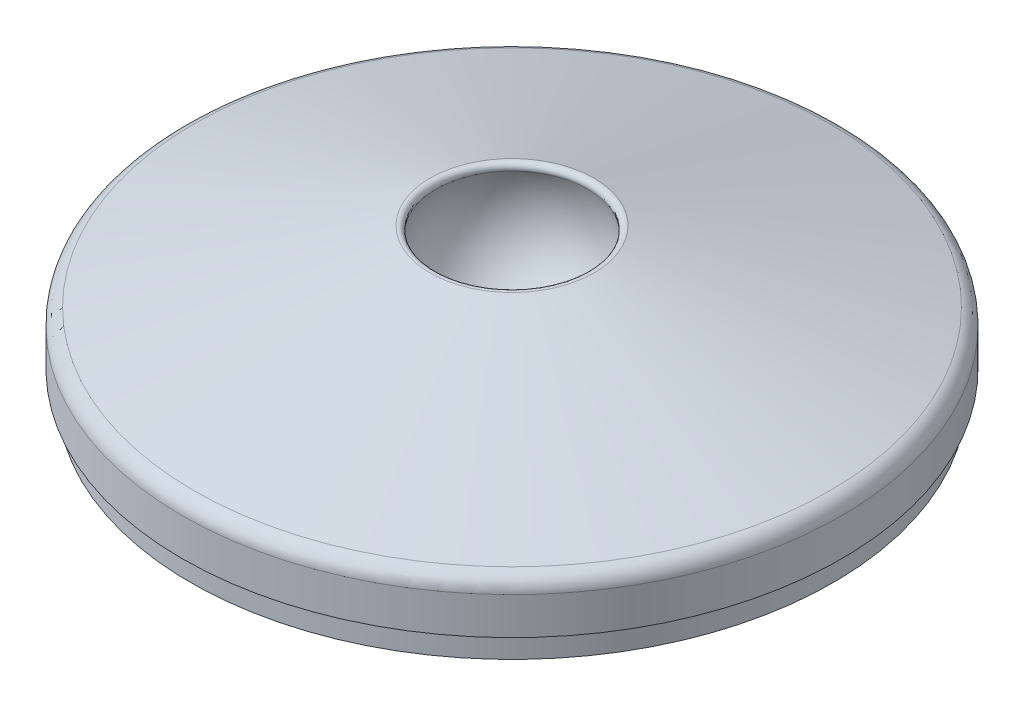
SolidWorks part; units mm, degrees
ref_plane "Front Plane" through (0, 0, 0) normal (0, 0, 1) x (1, 0, 0)
ref_plane "Top Plane" through (0, 0, 0) normal (0, 1, 0) x (1, 0, 0)
ref_plane "Right Plane" through (0, 0, 0) normal (1, 0, 0) x (0, 0, -1)
sketch "Sketch2" plane through (0, 0, 0) normal (0, 0, 1) x (1, 0, 0)
  line L0 (0, 35.0246) -> (0, -24.0887) construction
  line L1 (0, 0) -> (-20, 0)
  line L2 (-20, 0) -> (-20, 3.0049)
  line L3 (-20, 3.0049) -> (0, 9.0148)
  line L4 (0, 0) -> (0, 9.0148)
  dimension "D1" = 40
revolve "Revolve1" add sketch "Sketch2" angle 360 about L0
sketch "Sketch3" plane through (0, 0, 0) normal (0, 0, 1) x (1, 0, 0)
  line L1 (0, 12.2967) -> (0, -4.4445) construction
  line L2 (0, 0.2) -> (0, 10.2)
  line L3 (-20, 0) -> (20, 0) construction
  arc A0 (0, 10.2) -> (0, 0.2) centre (0, 5.2) ccw
  dimension "D1" = 10
  dimension "D2" = 5.2
revolve "Cut-Revolve2" cut sketch "Sketch3" angle 360 about L1
fillet "Fillet1" radius 0.3 1 edges at (0, 7.7165, 4.3206)
sketch "Sketch4" plane through (0, 0, 0) normal (0, -1, 0) x (1, 0, 0)
  circle A0 centre (0, 0) radius 19.5
  dimension "D1" = 39
extrude "Boss-Extrude1" add sketch "Sketch4" along normal blind 1.5
fillet "Fillet2" radius 1 1 edges at (0, 3.0049, 20)
